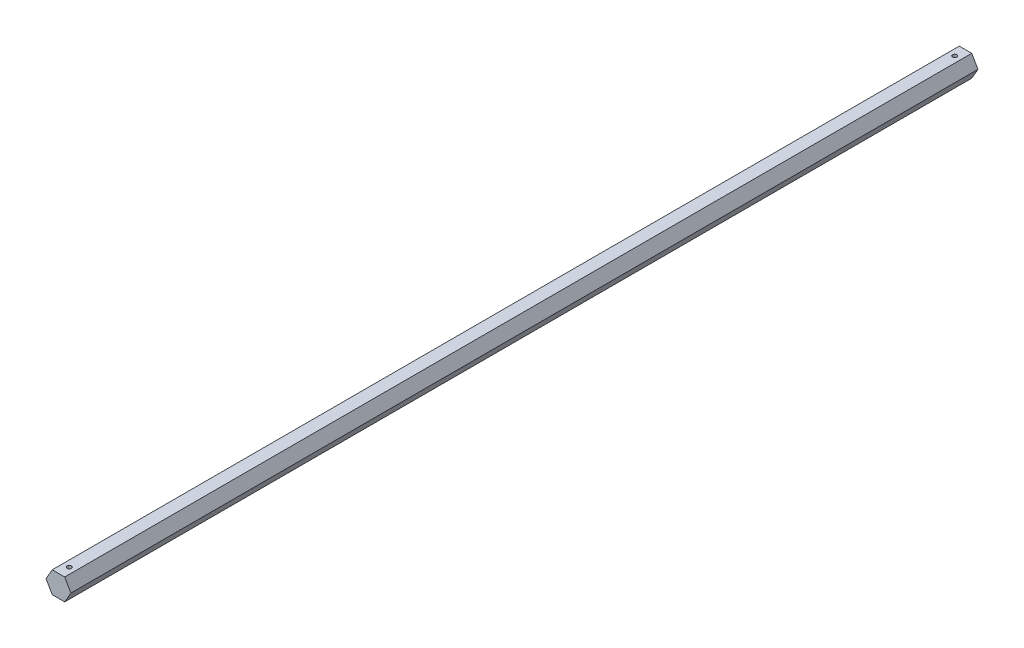
SolidWorks part; units mm, degrees
material "6061-T6 (SS)"
ref_plane "Front Plane" through (0, 0, 0) normal (0, 0, 1) x (1, 0, 0)
ref_plane "Top Plane" through (0, 0, 0) normal (0, 1, 0) x (1, 0, 0)
ref_plane "Right Plane" through (0, 0, 0) normal (1, 0, 0) x (0, 0, -1)
sketch "Sketch1" plane through (0, 0, 0) normal (0, 0, 1) x (1, 0, 0)
  line L1 (3.6662, -6.35) -> (7.3323, 0)
  line L2 (7.3323, 0) -> (3.6662, 6.35)
  line L3 (3.6662, 6.35) -> (-3.6662, 6.35)
  line L4 (-3.6662, 6.35) -> (-7.3323, 0)
  line L5 (-7.3323, 0) -> (-3.6662, -6.35)
  line L6 (-3.6662, -6.35) -> (3.6662, -6.35)
  circle A0 centre (0, 0) radius 7.3323 construction
  circle A1 centre (0, 0) radius 6.35 construction
  dimension "D1" = 12.7
extrude "Boss-Extrude1" add sketch "Sketch1" along normal mid plane 533.4
sketch "Sketch2" plane through (0, 6.35, 0) normal (0, 1, 0) x (1, 0, 0)
  line L0 (0, -266.7) -> (0, -260.35) construction
  line L1 (3.6662, -266.7) -> (-3.6662, -266.7) construction
  line L2 (-37.2354, 0) -> (83.5427, 0) construction
  line L3 (0, 266.7) -> (0, 260.35) construction
  circle A0 centre (0, -260.35) radius 1.2573
  circle A1 centre (0, 260.35) radius 1.2573
  dimension "D1" = 2.5146
  dimension "D2" = 260.35
extrude "Cut-Extrude1" cut sketch "Sketch2" against normal through all
